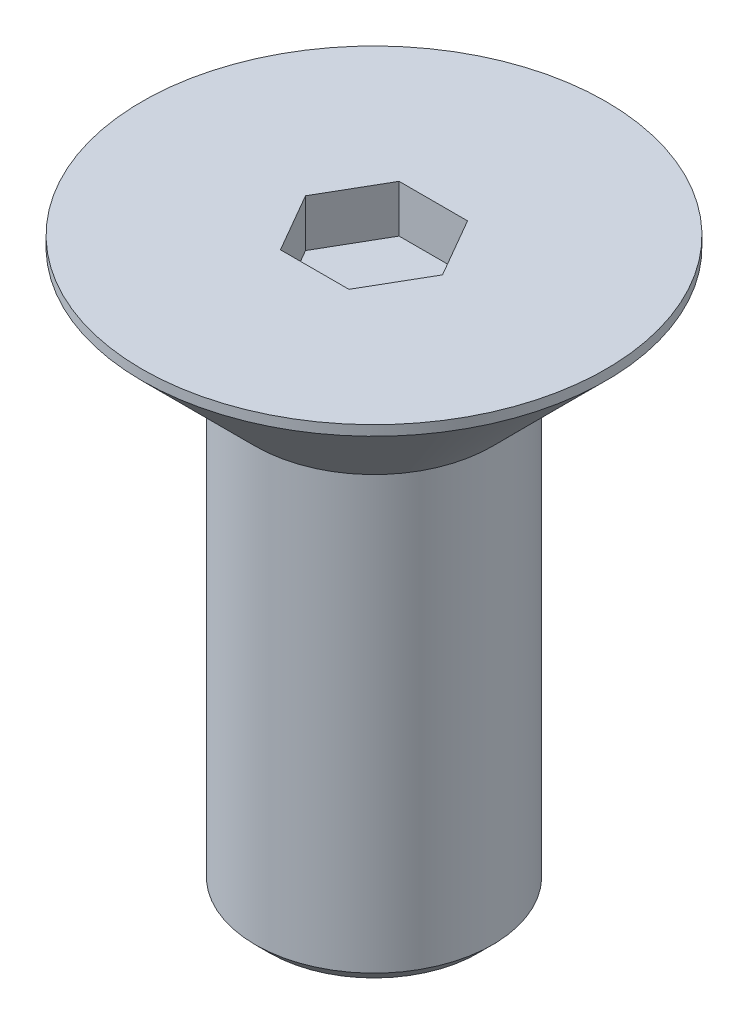
SolidWorks part; units mm, degrees
material "acero"
ref_plane "Alzado" through (0, 0, 0) normal (0, 0, 1) x (1, 0, 0)
ref_plane "Planta" through (0, 0, 0) normal (0, 1, 0) x (1, 0, 0)
ref_plane "Vista lateral" through (0, 0, 0) normal (1, 0, 0) x (0, 0, -1)
sketch "Croquis1" plane through (0, 0, 0) normal (0, 0, 1) x (1, 0, 0)
  line L0 (0, 0) -> (0, -60.9498) construction
  line L1 (0, 0) -> (5.1, 0)
  line L2 (2.5, -2.6) -> (5.1, 0)
  line L4 (2.5, -2.6) -> (2.5, -12)
  line L5 (2.5, -12) -> (0, -12)
  line L6 (0, -12) -> (0, 0)
  dimension "D1" = 12
  dimension "D2" = 45
  dimension "D3" = 2.6
  dimension "D4" = 5
revolve "Revolución1" add sketch "Croquis1" angle 360 about L0
chamfer "Chaflán2" distance 0.3 angle 45 1 edges at (0, 0, 5.1)
chamfer "Chaflán3" distance 0.3 angle 45 1 edges at (0, -12, 2.5)
sketch "Croquis3" plane through (0, 0, 0) normal (0, 1, 0) x (1, 0, 0)
  line L1 (-0.7217, 1.25) -> (-1.4434, 0)
  line L2 (-1.4434, 0) -> (-0.7217, -1.25)
  line L3 (-0.7217, -1.25) -> (0.7217, -1.25)
  line L4 (0.7217, -1.25) -> (1.4434, 0)
  line L5 (1.4434, 0) -> (0.7217, 1.25)
  line L6 (0.7217, 1.25) -> (-0.7217, 1.25)
  circle A0 centre (0, 0) radius 1.25 construction
  dimension "D1" = 2.5
extrude "Cortar-Extruir2" cut sketch "Croquis3" against normal blind 1
